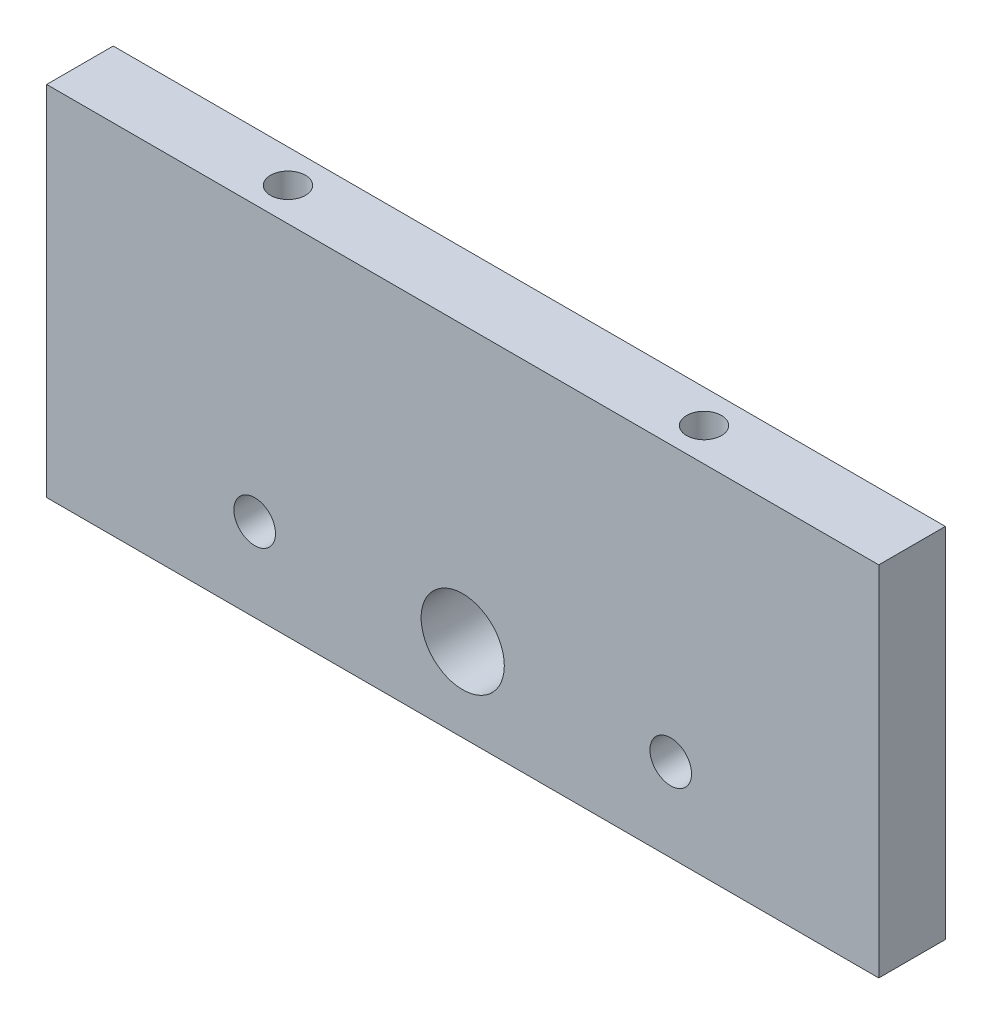
SolidWorks part; units mm, degrees
ref_plane "前视基准面" through (0, 0, 0) normal (0, 0, 1) x (1, 0, 0)
ref_plane "上视基准面" through (0, 0, 0) normal (0, 1, 0) x (1, 0, 0)
ref_plane "右视基准面" through (0, 0, 0) normal (1, 0, 0) x (0, 0, -1)
sketch "草图2" plane through (0, 0, 0) normal (0, 0, 1) x (1, 0, 0)
  line L1 (0, 0) -> (100, 0)
  line L2 (0, 0) -> (0, 43)
  line L3 (0, 43) -> (100, 43)
  line L4 (100, 0) -> (100, 43)
  dimension "D1" = 43
  dimension "D2" = 100
extrude "凸台-拉伸1" add sketch "草图2" along normal blind 8
sketch "草图3" plane through (0, 0, 8) normal (0, 0, 1) x (1, 0, 0)
  line L0 (50, 43) -> (50, 0) construction
  line L1 (100, 43) -> (0, 43) construction
  line L2 (0, 0) -> (100, 0) construction
  circle A0 centre (50, 10) radius 5
  dimension "D1" = 10
  dimension "D2" = 10
extrude "切除-拉伸1" cut sketch "草图3" against normal blind 8
hole_wizard "M6 螺纹孔1" positions "草图5" profile "草图6" tap size "M6" standard "ISO"
sketch "草图5" plane through (0, 0, 8) normal (0, 0, 1) x (1, 0, 0)
  line L0 (50, 43) -> (50, -5.0175) construction
  line L1 (100, 43) -> (0, 43) construction
  line L3 (0, 0) -> (100, 0) construction
  circle A0 centre (50, 10) radius 5 construction
  point P0 (25, 10)
  point P9 (75, 10)
  dimension "D1" = 25
  dimension "D2" = 10
sketch "草图6" plane through (25, 10, 8) normal (1, 0, 0) x (0, -1, 0)
  line L0 (0, 0) -> (0, 16.5022)
  line L1 (0, 16.5022) -> (2.5, 15)
  line L2 (2.5, 15) -> (2.5, 0)
  line L5 (2.5, 0) -> (0, 0)
  line L10 (0, 16.5022) -> (-2.5, 15) construction
  line L11 (0, -6.35) -> (0, 107.95) construction
  dimension "螺纹孔钻头直径" = 5
  dimension "螺纹孔钻头深度" = 15
  dimension "导头角度" = 118
cosmetic thread "孔螺蚊线1" parameters "D1"=8, "D2"=6
cosmetic thread "孔螺蚊线2" parameters "D1"=8, "D2"=6
hole_wizard "M5 螺纹孔1" positions "草图7" profile "草图8" tap size "M5" standard "ISO"
sketch "草图7" plane through (0, 43, 0) normal (0, 1, 0) x (1, 0, 0)
  line L0 (50, 0) -> (50, -8) construction
  line L1 (100, 0) -> (0, 0) construction
  line L2 (100, -8) -> (0, -8) construction
  line L3 (50, -8) -> (50, -4) construction
  line L4 (50, -4) -> (82.0894, -4) construction
  point P0 (25, -4)
  point P2 (75, -4)
  point P17 (0, 0)
  point P18 (0, 0)
  point P19 (0, 0)
  point P21 (0, 0)
  dimension "D1" = 50
sketch "草图8" plane through (25, 43, 4) normal (1, 0, 0) x (0, 0, 1)
  line L0 (0, 0) -> (0, 13.6618)
  line L1 (0, 13.6618) -> (2.1, 12.4)
  line L2 (2.1, 12.4) -> (2.1, 0)
  line L5 (2.1, 0) -> (0, 0)
  line L10 (0, 13.6618) -> (-2.1, 12.4) construction
  line L11 (0, -6.35) -> (0, 107.95) construction
  dimension "螺纹孔钻头直径" = 4.2
  dimension "螺纹孔钻头深度" = 12.4
  dimension "导头角度" = 118
cosmetic thread "孔螺蚊线3" parameters "D1"=10, "D2"=5
cosmetic thread "孔螺蚊线4" parameters "D1"=10, "D2"=5
